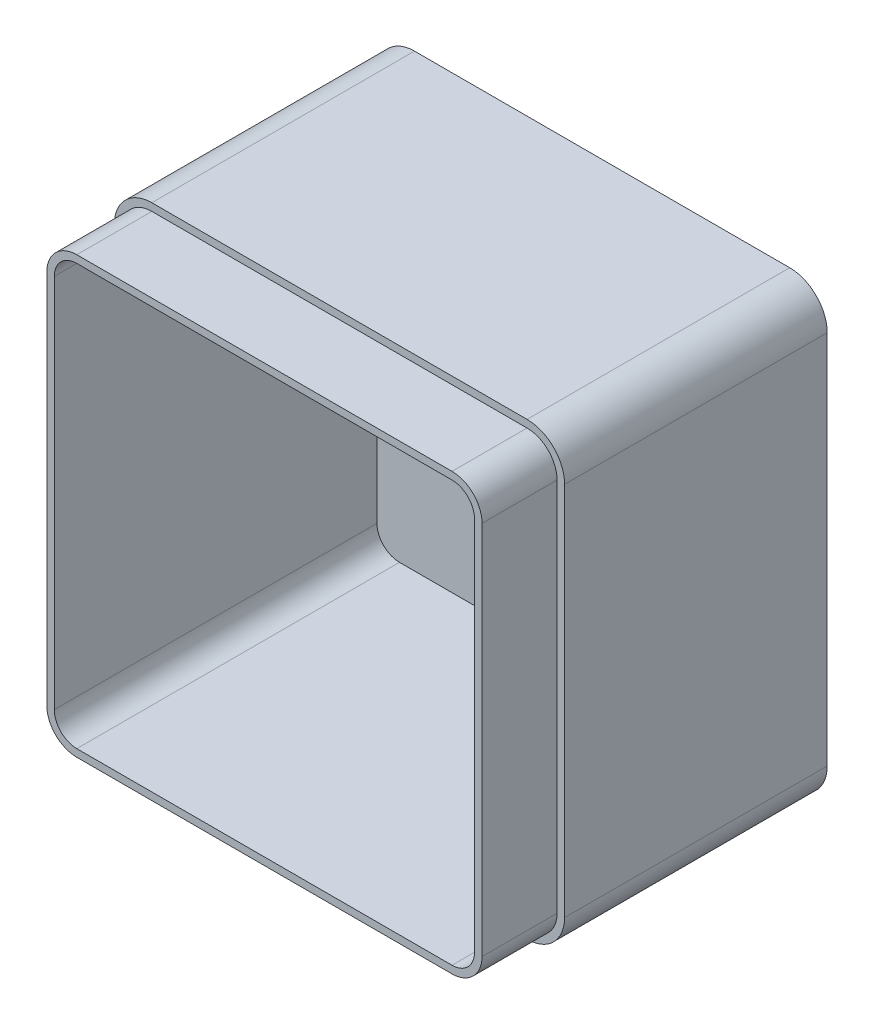
SolidWorks part; units mm, degrees
ref_plane "Front Plane" through (0, 0, 0) normal (0, 0, 1) x (1, 0, 0)
ref_plane "Top Plane" through (0, 0, 0) normal (0, 1, 0) x (1, 0, 0)
ref_plane "Right Plane" through (0, 0, 0) normal (1, 0, 0) x (0, 0, -1)
sketch "Sketch1" plane through (0, 0, 0) normal (0, 0, 1) x (1, 0, 0)
  line L1 (0, 0) -> (120, 0)
  line L2 (0, 0) -> (0, 120)
  line L3 (0, 120) -> (120, 120)
  line L4 (120, 0) -> (120, 120)
  dimension "D1" = 120
  dimension "D2" = 120
extrude "Boss-Extrude1" add sketch "Sketch1" along normal blind 90
fillet "Fillet1" radius 10 4 edges at (0, 0, 45) (120, 0, 45) (120, 120, 45) (0, 120, 45)
shell "Shell1" thickness 4
sketch "Sketch2" plane through (0, 0, 90) normal (0, 0, 1) x (1, 0, 0)
  line L0 (2, 110) -> (2, 10)
  line L1 (10, 2) -> (110, 2)
  line L2 (118, 10) -> (118, 110)
  line L3 (110, 118) -> (10, 118)
  line L4 (0, 110) -> (0, 10)
  line L5 (10, 0) -> (110, 0)
  line L6 (120, 10) -> (120, 110)
  line L7 (110, 120) -> (10, 120)
  line L8 (0, 110) -> (0, 10)
  line L9 (10, 0) -> (110, 0)
  line L10 (120, 10) -> (120, 110)
  line L11 (110, 120) -> (10, 120)
  arc A0 (2, 10) -> (10, 2) centre (10, 10) ccw
  arc A1 (110, 2) -> (118, 10) centre (110, 10) ccw
  arc A2 (118, 110) -> (110, 118) centre (110, 110) ccw
  arc A3 (10, 118) -> (2, 110) centre (10, 110) ccw
  arc A4 (0, 10) -> (10, 0) centre (10, 10) ccw
  arc A5 (110, 0) -> (120, 10) centre (110, 10) ccw
  arc A6 (120, 110) -> (110, 120) centre (110, 110) ccw
  arc A7 (10, 120) -> (0, 110) centre (10, 110) ccw
  arc A8 (0, 10) -> (10, 0) centre (10, 10) ccw
  arc A9 (110, 0) -> (120, 10) centre (110, 10) ccw
  arc A10 (120, 110) -> (110, 120) centre (110, 110) ccw
  arc A11 (10, 120) -> (0, 110) centre (10, 110) ccw
  dimension "D1" = 0
  dimension "D2" = 2
extrude "Cut-Extrude1" cut sketch "Sketch2" against normal blind 20
